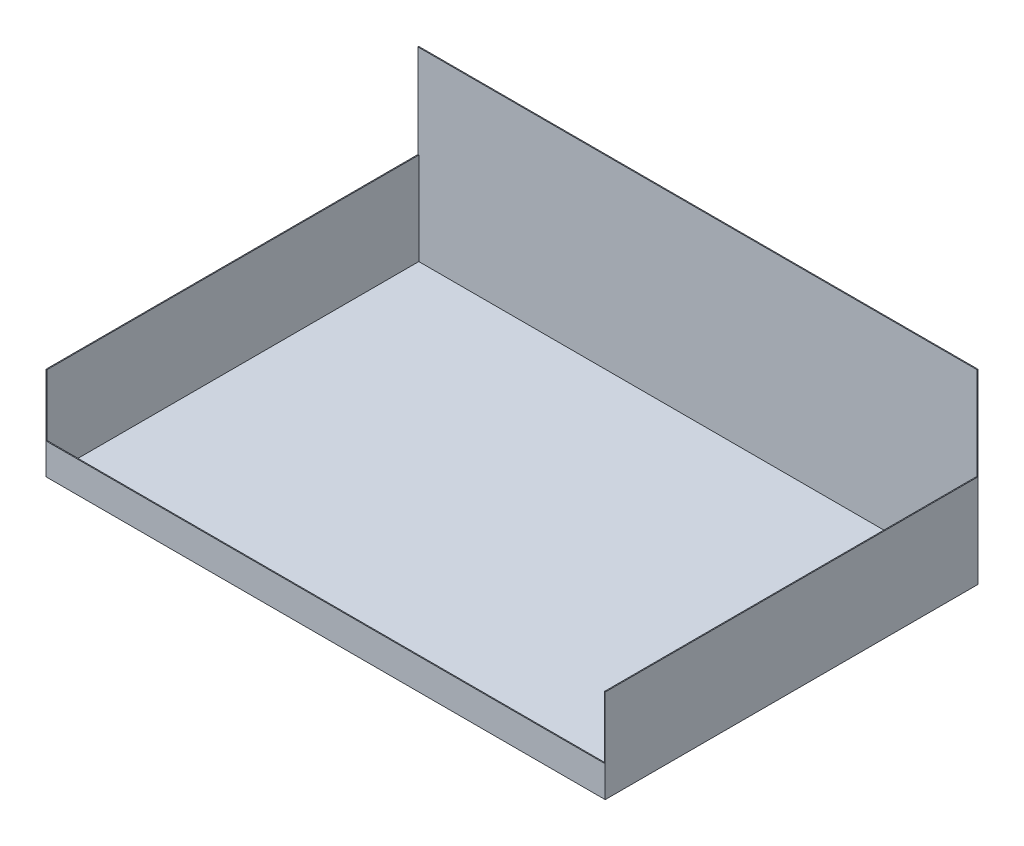
SolidWorks part; units mm, degrees
material "Custom Plastic"
ref_plane "Front Plane" through (0, 0, 0) normal (0, 0, 1) x (1, 0, 0)
ref_plane "Top Plane" through (0, 0, 0) normal (0, 1, 0) x (1, 0, 0)
ref_plane "Right Plane" through (0, 0, 0) normal (1, 0, 0) x (0, 0, -1)
sketch "Sketch2" plane through (0, 0, 0) normal (0, 0, 1) x (1, 0, 0)
  line L1 (-374.4681, 202.6596) -> (525.5319, 202.6596)
  line L2 (-374.4681, 202.6596) -> (-374.4681, -97.3404)
  line L3 (-374.4681, -97.3404) -> (525.5319, -97.3404)
  line L4 (525.5319, 202.6596) -> (525.5319, -97.3404)
  dimension "D1" = 900
  dimension "D2" = 300
extrude "Boss-Extrude1" add sketch "Sketch2" against normal blind 600
sketch "Sketch3" plane through (-374.4681, 0, 0) normal (-1, 0, 0) x (0, 0, 1)
  line L0 (-600, 202.6596) -> (-598.5, 202.6596)
  line L1 (-600, 202.6596) -> (0, 202.6596) construction
  line L2 (-598.5, 202.6596) -> (-598.5, 52.6596)
  line L3 (-598.5, 52.6596) -> (0, 52.6596)
  line L4 (0, 202.6596) -> (0, -97.3404) construction
  dimension "D1" = 1.5
  dimension "D2" = 150
extrude "Cut-Extrude1" cut sketch "Sketch3" against normal blind 900 and the other way through all
sketch "Sketch4" plane through (0, 0, 0) normal (0, 0, 1) x (1, 0, 0)
  line L0 (-374.4681, 52.6596) -> (-372.9681, 52.6596)
  line L1 (-374.4681, 52.6596) -> (525.5319, 52.6596) construction
  line L2 (-372.9681, 52.6596) -> (-372.9681, -47.3404)
  line L3 (-372.9681, -47.3404) -> (524.0319, -47.3404)
  line L4 (524.0319, -47.3404) -> (524.0319, 52.6596)
  line L5 (-374.4681, 52.6596) -> (525.5319, 52.6596) construction
  line L6 (524.0319, 52.6596) -> (525.5319, 52.6596)
  dimension "D1" = 1.5
  dimension "D2" = 1.5
  dimension "D3" = 100
extrude "Cut-Extrude2" cut sketch "Sketch4" against normal blind 598.5 and the other way through all
sketch "Sketch6" plane through (0, -47.3404, 0) normal (0, 1, 0) x (1, 0, 0)
  line L0 (-372.9681, 0) -> (-372.9681, 1.5)
  line L1 (-372.9681, 0) -> (-372.9681, 598.5) construction
  line L3 (-372.9681, 1.5) -> (524.0319, 1.5)
  line L4 (-372.9681, 1.5) -> (-372.9681, 598.5)
  line L5 (-372.9681, 598.5) -> (524.0319, 598.5)
  line L6 (524.0319, 1.5) -> (524.0319, 598.5)
  dimension "D1" = 1.5
extrude "Cut-Extrude4" cut sketch "Sketch6" against normal blind 48.5 contours L4 L3 L6 L5
